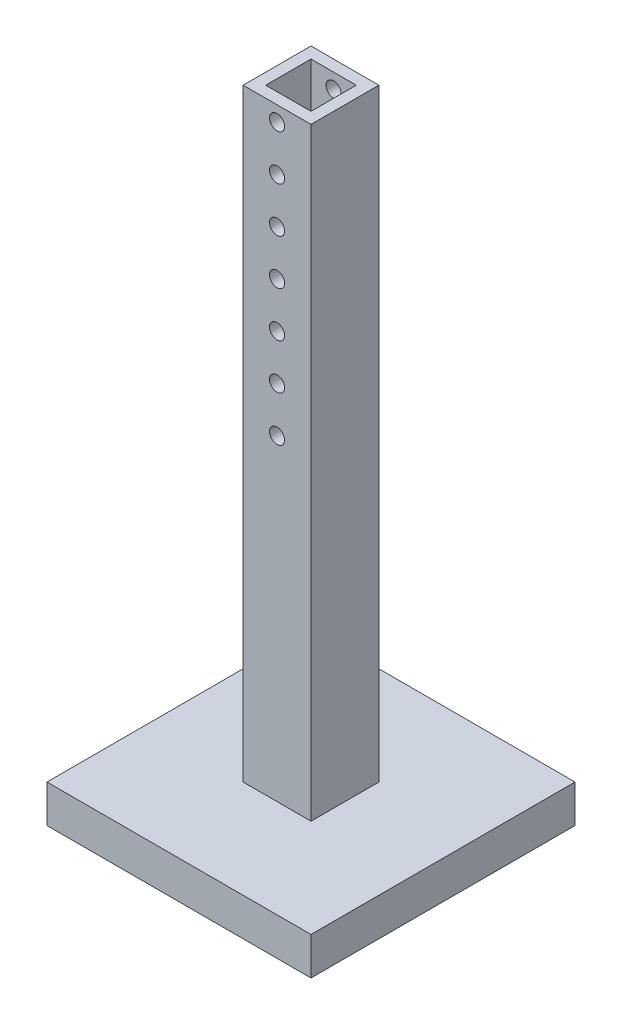
SolidWorks part; units mm, degrees
ref_plane "Front Plane" through (0, 0, 0) normal (0, 0, 1) x (1, 0, 0)
ref_plane "Top Plane" through (0, 0, 0) normal (0, 1, 0) x (1, 0, 0)
ref_plane "Right Plane" through (0, 0, 0) normal (1, 0, 0) x (0, 0, -1)
sketch "Sketch1" plane through (0, 0, 0) normal (0, 1, 0) x (1, 0, 0)
  line L1 (-175, 175) -> (175, 175)
  line L2 (-175, 175) -> (-175, -175)
  line L3 (-175, -175) -> (175, -175)
  line L4 (175, 175) -> (175, -175)
  line L5 (-175, 175) -> (175, -175) construction
  line L6 (-175, -175) -> (175, 175) construction
  point P0 (0, 0)
  dimension "D1" = 350
  dimension "D2" = 350
extrude "Boss-Extrude1" add sketch "Sketch1" along normal blind 50
sketch "Sketch2" plane through (0, 50, 0) normal (0, 1, 0) x (1, 0, 0)
  line L1 (-45, 45) -> (45, 45)
  line L2 (-45, 45) -> (-45, -45)
  line L3 (-45, -45) -> (45, -45)
  line L4 (45, 45) -> (45, -45)
  line L5 (-45, 45) -> (45, -45) construction
  line L6 (-45, -45) -> (45, 45) construction
  point P0 (0, 0)
  dimension "D1" = 90
  dimension "D2" = 90
extrude "Boss-Extrude2" add sketch "Sketch2" along normal blind 800
sketch "Sketch3" plane through (0, 850, 0) normal (0, 1, 0) x (1, 0, 0)
  line L0 (45, 45) -> (-45, 45) construction
  line L1 (-30, 30) -> (30, 30)
  line L2 (-30, 30) -> (-30, -30)
  line L3 (-30, -30) -> (30, -30)
  line L4 (30, 30) -> (30, -30)
  line L5 (-30, 30) -> (30, -30) construction
  line L6 (-30, -30) -> (30, 30) construction
  line L7 (-45, 45) -> (-45, -45) construction
  point P0 (0, 0)
  dimension "D1" = 15
  dimension "D2" = 15
extrude "Cut-Extrude1" cut sketch "Sketch3" against normal blind 800
sketch "Sketch4" plane through (0, 0, 45) normal (0, 0, 1) x (1, 0, 0)
  line L0 (-45, 850) -> (45, 850) construction
  circle A0 centre (0, 830) radius 10
  circle A1 centre (0, 770) radius 10
  circle A2 centre (0, 710) radius 10
  circle A3 centre (0, 650) radius 10
  circle A4 centre (0, 590) radius 10
  circle A5 centre (0, 530) radius 10
  circle A6 centre (0, 470) radius 10
  dimension "D2" = 20
  dimension "D3" = 7
  dimension "D1" = 20
extrude "Cut-Extrude3" cut sketch "Sketch4" against normal through all
